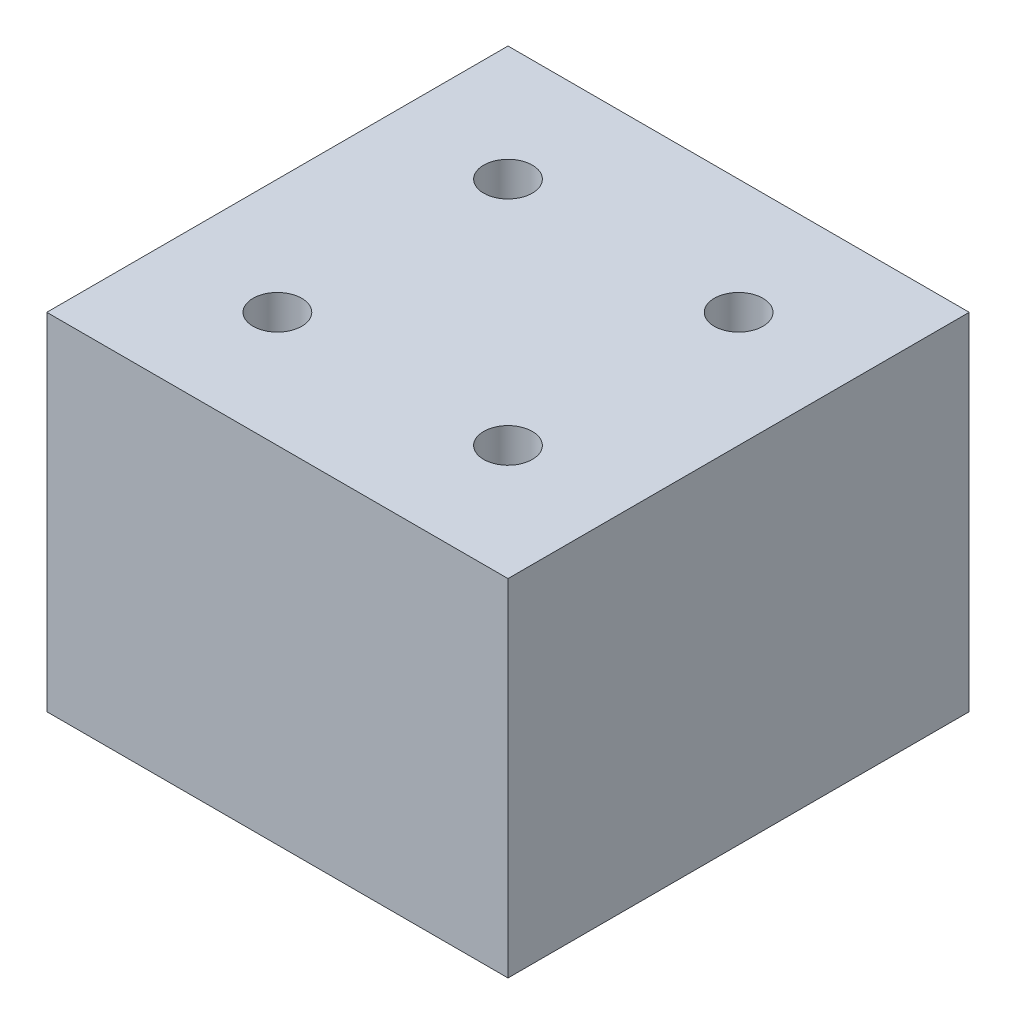
SolidWorks part; units mm, degrees
material "Plain Carbon Steel"
ref_plane "Front Plane" through (0, 0, 0) normal (0, 0, 1) x (1, 0, 0)
ref_plane "Top Plane" through (0, 0, 0) normal (0, 1, 0) x (1, 0, 0)
ref_plane "Right Plane" through (0, 0, 0) normal (1, 0, 0) x (0, 0, -1)
sketch "Sketch2" plane through (0, 0, 0) normal (0, 1, 0) x (1, 0, 0)
  line L1 (0, 0) -> (101.6, 0)
  line L2 (0, 0) -> (0, 101.6)
  line L3 (0, 101.6) -> (101.6, 101.6)
  line L4 (101.6, 0) -> (101.6, 101.6)
  dimension "D1" = 101.6
  dimension "D2" = 101.6
extrude "Boss-Extrude1" add sketch "Sketch2" along normal blind 76.2
hole_wizard "1/2-13 Tapped Hole4" positions "3DSketch6" profile "Sketch9" tap size "1/2-13" standard "ANSI Inch"
sketch3d "3DSketch6"
  line L0 (0, 76.2, -101.6) -> (0, 76.2, 0) construction
  line L1 (101.6, 76.2, 0) -> (101.6, 76.2, -101.6) construction
  line L2 (0, 76.2, 0) -> (101.6, 76.2, 0) construction
  line L3 (101.6, 76.2, -101.6) -> (0, 76.2, -101.6) construction
  point P0 (25.4, 76.2, -25.4)
  point P2 (25.4, 76.2, -76.2)
  point P4 (76.2, 76.2, -76.2)
  point P6 (76.2, 76.2, -25.4)
  dimension "D1" = 25.4
  dimension "D2" = 25.4
  dimension "D3" = 25.4
  dimension "D4" = 25.4
  dimension "D5" = 25.4
  dimension "D6" = 25.4
  dimension "D7" = 25.4
  dimension "D8" = 25.4
cosmetic thread "Hole Thread1"
cosmetic thread "Hole Thread2"
cosmetic thread "Hole Thread3"
cosmetic thread "Hole Thread4"
sketch "Sketch9" plane through (25.4, 76.2, -25.4) normal (1, 0, 0) x (0, 0, 1)
  line L0 (0, 0) -> (0, 38.2715)
  line L1 (0, 38.2715) -> (5.3581, 35.052)
  line L2 (5.3581, 35.052) -> (5.3581, 0)
  line L5 (5.3581, 0) -> (0, 0)
  line L10 (0, 38.2715) -> (-5.3581, 35.052) construction
  line L11 (0, -6.35) -> (0, 107.95) construction
  dimension "Tap Drill Dia." = 10.7163
  dimension "Tap Drill Depth" = 35.052
  dimension "Drill Angle" = 118
